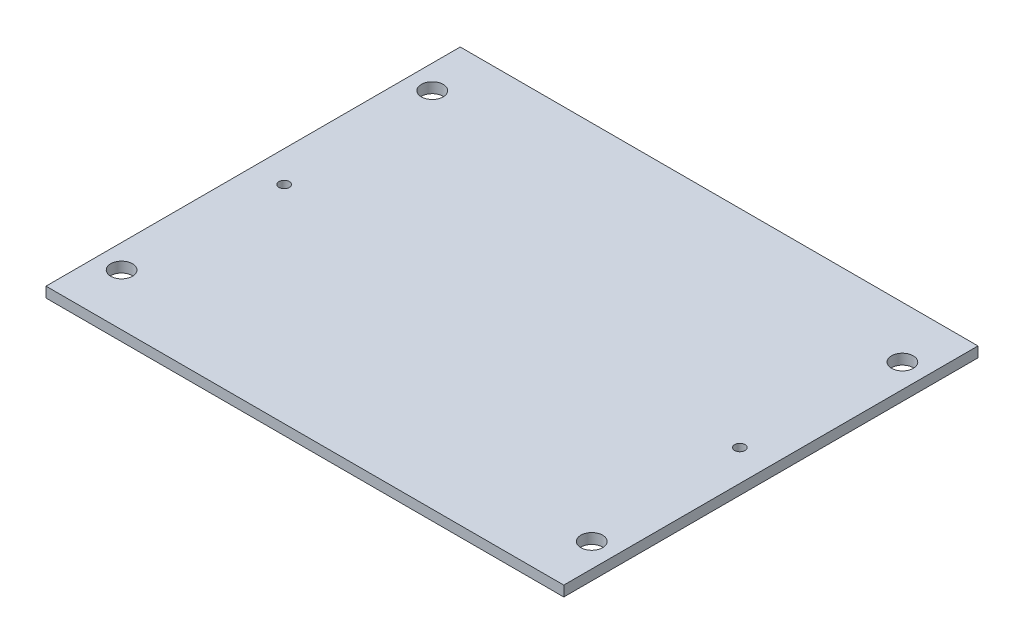
SolidWorks part; units mm, degrees
ref_plane "Front Plane" through (0, 0, 0) normal (0, 0, 1) x (1, 0, 0)
ref_plane "Top Plane" through (0, 0, 0) normal (0, 1, 0) x (1, 0, 0)
ref_plane "Right Plane" through (0, 0, 0) normal (1, 0, 0) x (0, 0, -1)
sketch "Sketch1" plane through (0, 0, 0) normal (0, 1, 0) x (1, 0, 0)
  line L1 (-250, -200) -> (250, -200)
  line L2 (-250, -200) -> (-250, 200)
  line L3 (-250, 200) -> (250, 200)
  line L4 (250, -200) -> (250, 200)
  line L5 (-250, -200) -> (250, 200) construction
  line L6 (-250, 200) -> (250, -200) construction
  circle A0 centre (-227, 150) radius 10.5
  circle A1 centre (-227, -150) radius 10.5
  circle A2 centre (227, -150) radius 10.5
  circle A3 centre (227, 150) radius 10.5
  circle A6 centre (-220, 0) radius 5
  circle A7 centre (220, 0) radius 5
  point P0 (0, 0)
  dimension "D3" = 300
  dimension "D4" = 50
  dimension "D5" = 50
  dimension "D6" = 50
  dimension "D7" = 50
  dimension "D8" = 23
  dimension "D9" = 23
  dimension "D10" = 454
  dimension "D11" = 23
  dimension "D12" = 23
  dimension "D13" = 454
  dimension "D14" = 21
  dimension "D15" = 21
  dimension "D16" = 21
  dimension "D17" = 21
  dimension "D21" = 10
  dimension "D22" = 30
  dimension "D23" = 10
  dimension "D24" = 30
  dimension "D25" = 200
  dimension "D26" = 200
  dimension "D1" = 500
  dimension "D2" = 400
extrude "Boss-Extrude1" add sketch "Sketch1" along normal blind 10
